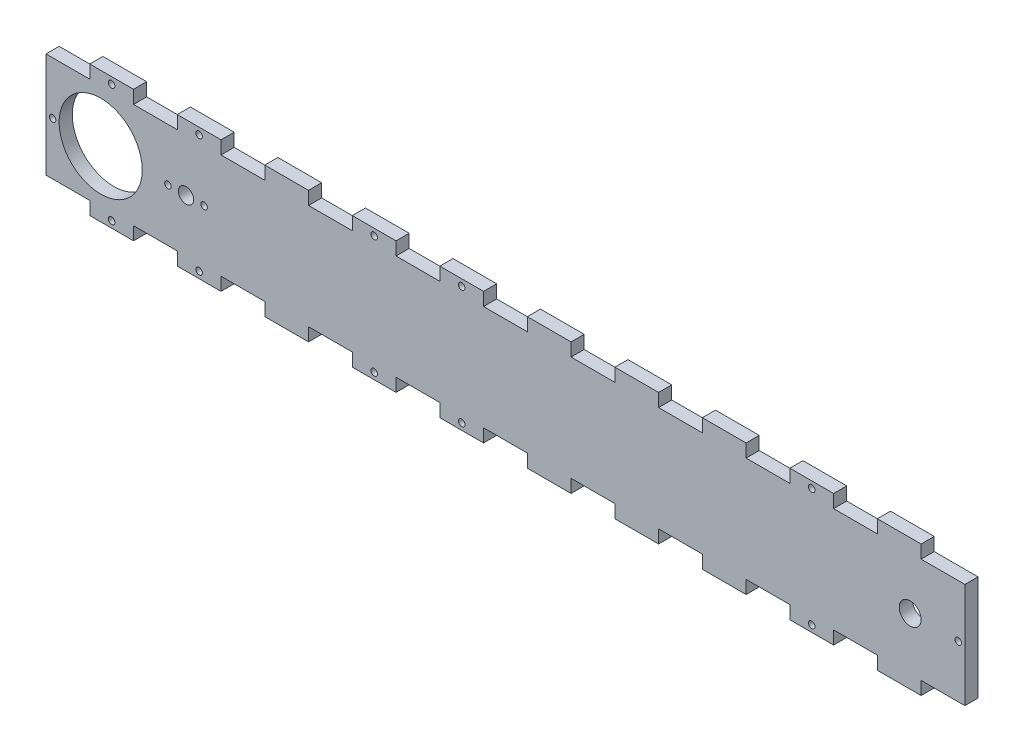
SolidWorks part; units mm, degrees
ref_plane "Plan de face" through (0, 0, 0) normal (0, 0, 1) x (1, 0, 0)
ref_plane "Plan de dessus" through (0, 0, 0) normal (0, 1, 0) x (1, 0, 0)
ref_plane "Plan de droite" through (0, 0, 0) normal (1, 0, 0) x (0, 0, -1)
sketch "Esquisse1" plane through (0, 0, 0) normal (0, 0, 1) x (1, 0, 0)
  line L0 (-82.8461, 16.5909) -> (-82.8461, -43.4091)
  dimension "D1" = 60
sketch "Esquisse2" plane through (0, 0, 0) normal (0, 0, 1) x (1, 0, 0)
  line L0 (-82.8461, -43.4091) -> (-62.8461, -43.4091)
  line L1 (-62.8461, -43.4091) -> (-62.8461, -37.4091)
  line L2 (-62.8461, -37.4091) -> (-42.8461, -37.4091)
  line L3 (-42.8461, -37.4091) -> (-42.8461, -43.4091)
  line L4 (-82.8461, -43.4091) -> (-82.8461, 16.5909)
  line L5 (-42.8461, -43.4091) -> (-22.8461, -43.4091)
  line L6 (-22.8461, -43.4091) -> (-22.8461, -37.4091)
  line L7 (-22.8461, -37.4091) -> (-2.8461, -37.4091)
  line L8 (-2.8461, -37.4091) -> (-2.8461, -43.4091)
  line L9 (-2.8461, -43.4091) -> (17.1539, -43.4091)
  line L10 (17.1539, -43.4091) -> (17.1539, -37.4091)
  line L11 (17.1539, -37.4091) -> (37.1539, -37.4091)
  line L12 (37.1539, -37.4091) -> (37.1539, -43.4091)
  line L13 (37.1539, -43.4091) -> (57.1539, -43.4091)
  line L14 (57.1539, -43.4091) -> (57.1539, -37.4091)
  line L15 (57.1539, -37.4091) -> (77.1539, -37.4091)
  line L16 (77.1539, -37.4091) -> (77.1539, -43.4091)
  line L17 (77.1539, -43.4091) -> (97.1539, -43.4091)
  line L18 (97.1539, -43.4091) -> (97.1539, -37.4091)
  line L19 (97.1539, -37.4091) -> (117.1539, -37.4091)
  line L20 (117.1539, -37.4091) -> (117.1539, -43.4091)
  line L21 (117.1539, -43.4091) -> (137.1539, -43.4091)
  line L22 (137.1539, -43.4091) -> (137.1539, -37.4091)
  line L23 (137.1539, -37.4091) -> (157.1539, -37.4091)
  line L24 (157.1539, -37.4091) -> (157.1539, -43.4091)
  line L25 (157.1539, -43.4091) -> (177.1539, -43.4091)
  line L26 (177.1539, -43.4091) -> (177.1539, -37.4091)
  line L27 (177.1539, -37.4091) -> (197.1539, -37.4091)
  line L28 (197.1539, -37.4091) -> (197.1539, -43.4091)
  line L29 (197.1539, -43.4091) -> (217.1539, -43.4091)
  line L30 (217.1539, -43.4091) -> (217.1539, -37.4091)
  line L31 (217.1539, -37.4091) -> (237.1539, -37.4091)
  line L32 (237.1539, -37.4091) -> (237.1539, -43.4091)
  line L33 (237.1539, -43.4091) -> (257.1539, -43.4091)
  line L34 (257.1539, -43.4091) -> (257.1539, -37.4091)
  line L35 (257.1539, -37.4091) -> (277.1539, -37.4091)
  line L36 (277.1539, -37.4091) -> (277.1539, -43.4091)
  line L37 (277.1539, -43.4091) -> (297.1539, -43.4091)
  line L38 (297.1539, -43.4091) -> (297.1539, -37.4091)
  line L39 (297.1539, -37.4091) -> (317.1539, -37.4091)
  line L40 (317.1539, -37.4091) -> (317.1539, -43.4091)
  line L41 (-214.7588, -13.4091) -> (445.6103, -13.4091) construction
  line L42 (77.1539, 10.5909) -> (77.1539, 16.5909)
  line L43 (317.1539, 10.5909) -> (317.1539, 16.5909)
  line L44 (297.1539, 10.5909) -> (317.1539, 10.5909)
  line L45 (297.1539, 16.5909) -> (297.1539, 10.5909)
  line L46 (277.1539, 16.5909) -> (297.1539, 16.5909)
  line L47 (277.1539, 10.5909) -> (277.1539, 16.5909)
  line L48 (257.1539, 16.5909) -> (257.1539, 10.5909)
  line L49 (257.1539, 10.5909) -> (277.1539, 10.5909)
  line L50 (237.1539, 16.5909) -> (257.1539, 16.5909)
  line L51 (237.1539, 10.5909) -> (237.1539, 16.5909)
  line L52 (217.1539, 16.5909) -> (217.1539, 10.5909)
  line L53 (217.1539, 10.5909) -> (237.1539, 10.5909)
  line L54 (197.1539, 16.5909) -> (217.1539, 16.5909)
  line L55 (197.1539, 10.5909) -> (197.1539, 16.5909)
  line L56 (177.1539, 16.5909) -> (177.1539, 10.5909)
  line L57 (177.1539, 10.5909) -> (197.1539, 10.5909)
  line L58 (157.1539, 16.5909) -> (177.1539, 16.5909)
  line L59 (157.1539, 10.5909) -> (157.1539, 16.5909)
  line L60 (137.1539, 16.5909) -> (137.1539, 10.5909)
  line L61 (137.1539, 10.5909) -> (157.1539, 10.5909)
  line L62 (117.1539, 16.5909) -> (137.1539, 16.5909)
  line L63 (117.1539, 10.5909) -> (117.1539, 16.5909)
  line L64 (97.1539, 16.5909) -> (97.1539, 10.5909)
  line L65 (97.1539, 10.5909) -> (117.1539, 10.5909)
  line L66 (77.1539, 16.5909) -> (97.1539, 16.5909)
  line L67 (57.1539, 16.5909) -> (57.1539, 10.5909)
  line L68 (57.1539, 10.5909) -> (77.1539, 10.5909)
  line L69 (37.1539, 16.5909) -> (57.1539, 16.5909)
  line L70 (37.1539, 10.5909) -> (37.1539, 16.5909)
  line L71 (17.1539, 16.5909) -> (17.1539, 10.5909)
  line L72 (17.1539, 10.5909) -> (37.1539, 10.5909)
  line L73 (-2.8461, 16.5909) -> (17.1539, 16.5909)
  line L74 (-2.8461, 10.5909) -> (-2.8461, 16.5909)
  line L75 (-22.8461, 16.5909) -> (-22.8461, 10.5909)
  line L76 (-22.8461, 10.5909) -> (-2.8461, 10.5909)
  line L77 (-42.8461, 10.5909) -> (-42.8461, 16.5909)
  line L78 (-62.8461, 16.5909) -> (-62.8461, 10.5909)
  line L79 (-82.8461, 16.5909) -> (-62.8461, 16.5909)
  line L80 (-62.8461, 10.5909) -> (-42.8461, 10.5909)
  line L81 (-42.8461, 16.5909) -> (-22.8461, 16.5909)
  line L82 (317.1539, -43.4091) -> (337.1539, -43.4091)
  line L83 (317.1539, 16.5909) -> (337.1539, 16.5909)
  line L84 (337.1539, 16.5909) -> (337.1539, -43.4091)
  dimension "D1" = 20
  dimension "D2" = 20
  dimension "D3" = 6
  dimension "D4" = 10
extrude "Boss.-Extru.1" add sketch "Esquisse2" along normal blind 6
sketch "Esquisse3" plane through (0, 0, 6) normal (0, 0, 1) x (1, 0, 0)
  line L0 (-82.8461, -13.4091) -> (-37.8461, -13.4091) construction
  line L1 (-82.8461, 16.5909) -> (-82.8461, -43.4091) construction
  line L2 (-37.8461, -13.4091) -> (-37.8461, -43.4091) construction
  line L3 (-42.8461, -43.4091) -> (-22.8461, -43.4091) construction
  circle A0 centre (-37.8461, -13.4091) radius 19
  dimension "D3" = 38
  dimension "D1" = 45
  dimension "D2" = 30
extrude "Enlèv. mat.-Extru.1" cut sketch "Esquisse3" against normal blind 10
sketch "Esquisse4" plane through (0, 0, 6) normal (0, 0, 1) x (1, 0, 0)
  line L1 (-82.8461, 16.5909) -> (-62.8461, 16.5909)
  line L2 (-82.8461, 16.5909) -> (-82.8461, -43.4091)
  line L3 (-82.8461, -43.4091) -> (-62.8461, -43.4091)
  line L4 (-62.8461, 16.5909) -> (-62.8461, -43.4091)
extrude "Enlèv. mat.-Extru.2" cut sketch "Esquisse4" against normal blind 10
sketch "Esquisse5" plane through (0, 0, 6) normal (0, 0, 1) x (1, 0, 0)
  line L0 (337.1539, -43.4091) -> (337.1539, 16.5909) construction
  line L1 (357.1539, 10.5909) -> (337.1539, 10.5909)
  line L2 (357.1539, 10.5909) -> (357.1539, -37.4091)
  line L3 (357.1539, -37.4091) -> (337.1539, -37.4091)
  line L4 (337.1539, 10.5909) -> (337.1539, -37.4091)
  dimension "D1" = 20
extrude "Boss.-Extru.2" add sketch "Esquisse5" against normal blind 6
sketch "Esquisse6" plane through (0, 0, 6) normal (0, 0, 1) x (1, 0, 0)
  line L0 (117.1539, -43.4091) -> (137.1539, -43.4091) construction
  line L1 (17.1539, 16.5909) -> (-2.8461, 16.5909) construction
  circle A0 centre (127.1539, -40.4091) radius 1.5
  circle A1 centre (287.1539, -40.4091) radius 1.5
  circle A2 centre (7.1539, -40.4091) radius 1.5
  circle A3 centre (7.1539, 13.5909) radius 1.5
  circle A4 centre (127.1539, 13.5909) radius 1.5
  circle A5 centre (287.1539, 13.5909) radius 1.5
  dimension "D2" = 3
  dimension "D3" = 3
  dimension "D4" = 3
  dimension "D6" = 3
  dimension "D7" = 3
  dimension "D8" = 3
  dimension "D1" = 3
  dimension "D5" = 3
extrude "Enlèv. mat.-Extru.3" cut sketch "Esquisse6" against normal blind 10
sketch "Esquisse7" plane through (0, 0, 6) normal (0, 0, 1) x (1, 0, 0)
  line L0 (-62.8461, -37.4091) -> (-62.8461, 10.5909) construction
  circle A0 centre (-59.8461, -13.4091) radius 1.5
  dimension "D1" = 3
  dimension "D2" = 3
extrude "Enlèv. mat.-Extru.4" cut sketch "Esquisse7" against normal blind 10
sketch "Esquisse8" plane through (0, 0, 6) normal (0, 0, 1) x (1, 0, 0)
  line L0 (357.1539, -37.4091) -> (357.1539, 10.5909) construction
  circle A0 centre (354.1539, -13.4091) radius 1.5
  dimension "D1" = 3
  dimension "D2" = 3
extrude "Enlèv. mat.-Extru.5" cut sketch "Esquisse8" against normal blind 10
sketch "Esquisse9" plane through (0, 0, 6) normal (0, 0, 1) x (1, 0, 0)
  line L0 (-32.8461, 16.5909) -> (-32.8461, 10.5909) construction
  line L1 (-22.8461, 16.5909) -> (-42.8461, 16.5909) construction
  line L2 (-32.8461, -43.4091) -> (-32.8461, -37.4091) construction
  line L4 (-42.8461, -43.4091) -> (-22.8461, -43.4091) construction
  line L5 (-37.8461, -13.4091) -> (1.1539, -13.4091) construction
  line L6 (-7.0961, -13.4091) -> (9.4039, -13.4091)
  circle A0 centre (-32.8461, 13.5909) radius 1.5
  circle A1 centre (-32.8461, -40.4091) radius 1.5
  circle A2 centre (1.1539, -13.4091) radius 3.5
  circle A3 centre (-7.0961, -13.4091) radius 1.5
  circle A4 centre (9.4039, -13.4091) radius 1.5
  point P19 (1.1539, -13.4091)
  dimension "D1" = 3
  dimension "D2" = 3
  dimension "D4" = 7
  dimension "D6" = 3
  dimension "D7" = 3
  dimension "D3" = 39
  dimension "D5" = 16.5
extrude "Enlèv. mat.-Extru.6" cut sketch "Esquisse9" against normal blind 10
sketch "Esquisse10" plane through (0, 0, 6) normal (0, 0, 1) x (1, 0, 0)
  line L0 (-32.8461, 16.5909) -> (-32.8461, 10.5909) construction
  line L1 (-22.8461, 16.5909) -> (-42.8461, 16.5909) construction
  line L2 (-32.8461, -43.4091) -> (-32.8461, -37.4091) construction
  line L3 (-42.8461, -43.4091) -> (-22.8461, -43.4091) construction
  circle A0 centre (-32.8461, 13.5909) radius 1.5
  circle A1 centre (-32.8461, -40.4091) radius 1.5
  dimension "D1" = 3
  dimension "D2" = 3
extrude "Enlèv. mat.-Extru.7" cut sketch "Esquisse10" against normal blind 10
sketch "Esquisse11" plane through (0, 0, 6) normal (0, 0, 1) x (1, 0, 0)
  line L0 (87.1539, 10.5909) -> (87.1539, 16.5909) construction
  line L1 (97.1539, 16.5909) -> (77.1539, 16.5909) construction
  line L2 (87.1539, -37.4091) -> (87.1539, -43.4091) construction
  line L3 (77.1539, -43.4091) -> (97.1539, -43.4091) construction
  circle A0 centre (87.1539, 13.5909) radius 1.5
  circle A1 centre (87.1539, -40.4091) radius 1.5
  dimension "D1" = 3
  dimension "D2" = 3
extrude "Enlèv. mat.-Extru.8" cut sketch "Esquisse11" against normal blind 10
sketch "Esquisse13" plane through (0, 0, 6) normal (0, 0, 1) x (1, 0, 0)
  line L0 (357.1539, -13.4091) -> (332.1539, -13.4091) construction
  line L1 (357.1539, -37.4091) -> (357.1539, 10.5909) construction
  circle A0 centre (332.1539, -13.4091) radius 5
  dimension "D2" = 10
  dimension "D1" = 25
extrude "Enlèv. mat.-Extru.9" cut sketch "Esquisse13" against normal blind 10
